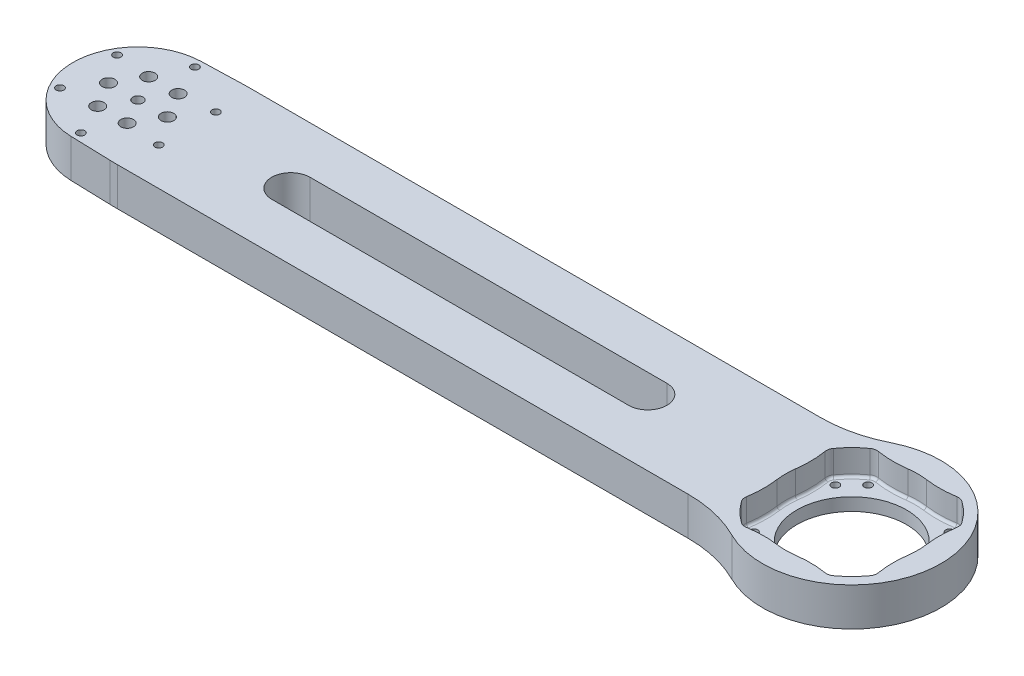
SolidWorks part; units mm, degrees
ref_plane "前视基准面" through (0, 0, 0) normal (0, 0, 1) x (1, 0, 0)
ref_plane "上视基准面" through (0, 0, 0) normal (0, 1, 0) x (1, 0, 0)
ref_plane "右视基准面" through (0, 0, 0) normal (1, 0, 0) x (0, 0, -1)
sketch "草图1" plane through (0, 0, 0) normal (0, 1, 0) x (1, 0, 0)
  line L0 (21.6852, 20) -> (239.1956, 20)
  line L1 (21.6852, -20) -> (239.1956, -20)
  line L2 (280, 35) -> (280, -35) construction
  line L3 (245, 0) -> (315, 0) construction
  line L4 (302.3882, -15.9693) -> (280, 0) construction
  line L5 (264.0307, 22.3882) -> (280, 0) construction
  line L8 (60, 0) -> (200, 0) construction
  line L9 (60, 7.5) -> (200, 7.5)
  line L10 (60, -7.5) -> (200, -7.5)
  line L11 (21.6852, 20) -> (21.6852, -20) construction
  circle A0 centre (0, 0) radius 25.5 construction
  circle A2 centre (280, 0) radius 35 construction
  circle A3 centre (280, 0) radius 27.5 construction
  circle A4 centre (302.3882, -15.9693) radius 1.5
  circle A5 centre (264.0307, 22.3882) radius 1.5
  circle A6 centre (302.3882, 15.9693) radius 1.5
  circle A7 centre (264.0307, -22.3882) radius 1.5
  circle A8 centre (280, 0) radius 35 construction
  circle A9 centre (295.9693, -22.3882) radius 1.5
  circle A10 centre (257.6118, 15.9693) radius 1.5
  circle A11 centre (280, 0) radius 35 construction
  circle A12 centre (257.6118, -15.9693) radius 1.5
  circle A13 centre (295.9693, 22.3882) radius 1.5
  circle A14 centre (280, 0) radius 35 construction
  circle A15 centre (280, 0) radius 21.5
  arc A18 (12.1533, 22.4176) -> (12.1533, -22.4176) centre (0, 0) ccw
  circle A19 centre (0, 0) radius 2
  arc A22 (60, 7.5) -> (60, -7.5) centre (60, 0) ccw
  arc A23 (200, -7.5) -> (200, 7.5) centre (200, 0) ccw
  arc A25 (257.3309, 26.6667) -> (257.3309, -26.6667) centre (280, 0) cw
  arc A26 (239.1956, -20) -> (257.3309, -26.6667) centre (239.1956, -48) cw
  arc A27 (239.1956, 20) -> (257.3309, 26.6667) centre (239.1956, 48) ccw
  arc A28 (21.6852, -20) -> (12.1533, -22.4176) centre (21.6852, -40) ccw
  arc A29 (21.6852, 20) -> (12.1533, 22.4176) centre (21.6852, 40) cw
  point P4 (21.6852, 0)
  point P36 (280, 0)
  point P39 (251.2772, -20)
  point P40 (294.1494, 32.0124)
  point P43 (130, 0)
  point P55 (251.2772, 20)
  point P66 (15.8193, -20)
  point P69 (15.8193, 20)
  dimension "D1" = 51
  dimension "D2" = 70
  dimension "D3" = 55
  dimension "D6" = 3
  dimension "D8" = 43
  dimension "D11" = 20
  dimension "D12" = 4
  dimension "D14" = 40
  dimension "D9" = 280
  dimension "D10" = 28
  dimension "D4" = 54.5
  dimension "D5" = 54.5
  dimension "D13" = 130
  dimension "D16" = 15
  dimension "D17" = 140
  dimension "D7" = 4
extrude "凸台-拉伸1" add sketch "草图1" along normal blind 15
sketch "草图2" plane through (0, 15, 0) normal (0, 1, 0) x (1, 0, 0)
  circle A0 centre (0, 0) radius 11.547 construction
  circle A1 centre (-11.547, 0) radius 1.7908
sketch "草图3" plane through (0, 15, 0) normal (0, 1, 0) x (1, 0, 0)
  circle A0 centre (-5.7735, -10) radius 2.5 construction
  circle A1 centre (-5.7735, -10) radius 2.5
  circle A2 centre (-11.547, 0) radius 2.5
  circle A3 centre (-5.7735, 10) radius 2.5
  circle A4 centre (5.7735, 10) radius 2.5
  circle A5 centre (11.547, 0) radius 2.5
  circle A6 centre (5.7735, -10) radius 2.5
  circle A7 centre (0, -22.375) radius 1.5
  circle A8 centre (-19.3773, -11.1875) radius 1.5
  circle A9 centre (-19.3773, 11.1875) radius 1.5
  circle A10 centre (0, 22.375) radius 1.5
  circle A11 centre (19.3773, 11.1875) radius 1.5
  circle A12 centre (19.3773, -11.1875) radius 1.5
  point P15 (0, 0)
  point P29 (0, 0)
  dimension "D1" = 6
  dimension "D2" = 6
extrude "切除-拉伸1" cut sketch "草图3" against normal through all
sketch "草图4" plane through (0, 15, 0) normal (0, 1, 0) x (1, 0, 0)
  arc A0 (283.6096, 25.6977) -> (295.3982, 25.8413) centre (289.0345, 64.3186) ccw
  arc A1 (295.9693, 25.8882) -> (295.3982, 25.8413) centre (295.9693, 22.3882) ccw
  arc A2 (298.0018, 25.2376) -> (295.9693, 25.8882) centre (295.9693, 22.3882) ccw
  arc A3 (305.2376, 18.0018) -> (298.0018, 25.2376) centre (280, 0) ccw
  arc A4 (305.8413, 15.3982) -> (305.2376, 18.0018) centre (302.3882, 15.9693) ccw
  arc A5 (305.8413, 15.3982) -> (305.6977, 3.6096) centre (344.3186, 9.0345) ccw
  arc A6 (305.6977, -3.6096) -> (305.6977, 3.6096) centre (280, 0) ccw
  arc A7 (305.6977, -3.6096) -> (305.8413, -15.3982) centre (344.3186, -9.0345) ccw
  arc A8 (305.2376, -18.0018) -> (305.8413, -15.3982) centre (302.3882, -15.9693) ccw
  arc A9 (298.0018, -25.2376) -> (305.2376, -18.0018) centre (280, 0) ccw
  arc A10 (295.3982, -25.8413) -> (298.0018, -25.2376) centre (295.9693, -22.3882) ccw
  arc A11 (295.3982, -25.8413) -> (289.0345, -25.3186) centre (289.0345, -64.3186) ccw
  arc A12 (289.0345, -25.3186) -> (283.6096, -25.6977) centre (289.0345, -64.3186) ccw
  arc A13 (276.3904, -25.6977) -> (283.6096, -25.6977) centre (280, 0) ccw
  arc A14 (276.3904, -25.6977) -> (270.9655, -25.3186) centre (270.9655, -64.3186) ccw
  arc A15 (270.9655, -25.3186) -> (264.6018, -25.8413) centre (270.9655, -64.3186) ccw
  arc A16 (261.9982, -25.2376) -> (264.6018, -25.8413) centre (264.0307, -22.3882) ccw
  arc A17 (254.7624, -18.0018) -> (261.9982, -25.2376) centre (280, 0) ccw
  arc A18 (254.1587, -15.3982) -> (254.7624, -18.0018) centre (257.6118, -15.9693) ccw
  arc A19 (254.1587, -15.3982) -> (254.3023, -3.6096) centre (215.6814, -9.0345) ccw
  arc A20 (254.3023, 3.6096) -> (254.3023, -3.6096) centre (280, 0) ccw
  arc A21 (254.3023, 3.6096) -> (254.1587, 15.3982) centre (215.6814, 9.0345) ccw
  arc A22 (254.7624, 18.0018) -> (254.1587, 15.3982) centre (257.6118, 15.9693) ccw
  arc A23 (261.9982, 25.2376) -> (254.7624, 18.0018) centre (280, 0) ccw
  arc A24 (264.0307, 25.8882) -> (261.9982, 25.2376) centre (264.0307, 22.3882) ccw
  arc A25 (264.6018, 25.8413) -> (264.0307, 25.8882) centre (264.0307, 22.3882) ccw
  arc A26 (264.6018, 25.8413) -> (276.3904, 25.6977) centre (270.9655, 64.3186) ccw
  arc A27 (280, 25.95) -> (276.3904, 25.6977) centre (280, 0) ccw
  arc A28 (283.6096, 25.6977) -> (280, 25.95) centre (280, 0) ccw
  arc A29 (283.4705, 24.7074) -> (295.5614, 24.8547) centre (289.0345, 64.3186) ccw
  arc A30 (295.9693, 24.8882) -> (295.5614, 24.8547) centre (295.9693, 22.3882) ccw
  arc A31 (297.4211, 24.4235) -> (295.9693, 24.8882) centre (295.9693, 22.3882) ccw
  arc A32 (304.4235, 17.4211) -> (297.4211, 24.4235) centre (280, 0) ccw
  arc A33 (304.8547, 15.5614) -> (304.4235, 17.4211) centre (302.3882, 15.9693) ccw
  arc A34 (304.8547, 15.5614) -> (304.7074, 3.4705) centre (344.3186, 9.0345) ccw
  arc A35 (304.7074, -3.4705) -> (304.7074, 3.4705) centre (280, 0) ccw
  arc A36 (304.7074, -3.4705) -> (304.8547, -15.5614) centre (344.3186, -9.0345) ccw
  arc A37 (304.4235, -17.4211) -> (304.8547, -15.5614) centre (302.3882, -15.9693) ccw
  arc A38 (297.4211, -24.4235) -> (304.4235, -17.4211) centre (280, 0) ccw
  arc A39 (295.5614, -24.8547) -> (297.4211, -24.4235) centre (295.9693, -22.3882) ccw
  arc A40 (295.5614, -24.8547) -> (289.0345, -24.3186) centre (289.0345, -64.3186) ccw
  arc A41 (289.0345, -24.3186) -> (283.4705, -24.7074) centre (289.0345, -64.3186) ccw
  arc A42 (276.5295, -24.7074) -> (283.4705, -24.7074) centre (280, 0) ccw
  arc A43 (276.5295, -24.7074) -> (270.9655, -24.3186) centre (270.9655, -64.3186) ccw
  arc A44 (270.9655, -24.3186) -> (264.4386, -24.8547) centre (270.9655, -64.3186) ccw
  arc A45 (262.5789, -24.4235) -> (264.4386, -24.8547) centre (264.0307, -22.3882) ccw
  arc A46 (255.5765, -17.4211) -> (262.5789, -24.4235) centre (280, 0) ccw
  arc A47 (255.1453, -15.5614) -> (255.5765, -17.4211) centre (257.6118, -15.9693) ccw
  arc A48 (255.1453, -15.5614) -> (255.2926, -3.4705) centre (215.6814, -9.0345) ccw
  arc A49 (255.2926, 3.4705) -> (255.2926, -3.4705) centre (280, 0) ccw
  arc A50 (255.2926, 3.4705) -> (255.1453, 15.5614) centre (215.6814, 9.0345) ccw
  arc A51 (255.5765, 17.4211) -> (255.1453, 15.5614) centre (257.6118, 15.9693) ccw
  arc A52 (262.5789, 24.4235) -> (255.5765, 17.4211) centre (280, 0) ccw
  arc A53 (264.0307, 24.8882) -> (262.5789, 24.4235) centre (264.0307, 22.3882) ccw
  arc A54 (264.4386, 24.8547) -> (264.0307, 24.8882) centre (264.0307, 22.3882) ccw
  arc A55 (264.4386, 24.8547) -> (276.5295, 24.7074) centre (270.9655, 64.3186) ccw
  arc A56 (280, 24.95) -> (276.5295, 24.7074) centre (280, 0) ccw
  arc A57 (283.4705, 24.7074) -> (280, 24.95) centre (280, 0) ccw
  arc A58 (283.4705, 24.7074) -> (295.5614, 24.8547) centre (289.0345, 64.3186) ccw construction
  arc A59 (295.9693, 24.8882) -> (295.5614, 24.8547) centre (295.9693, 22.3882) ccw construction
  arc A60 (297.4211, 24.4235) -> (295.9693, 24.8882) centre (295.9693, 22.3882) ccw construction
  arc A61 (304.4235, 17.4211) -> (297.4211, 24.4235) centre (280, 0) ccw construction
  arc A62 (304.8547, 15.5614) -> (304.4235, 17.4211) centre (302.3882, 15.9693) ccw construction
  arc A63 (304.8547, 15.5614) -> (304.7074, 3.4705) centre (344.3186, 9.0345) ccw construction
  arc A64 (304.7074, -3.4705) -> (304.7074, 3.4705) centre (280, 0) ccw construction
  arc A65 (304.7074, -3.4705) -> (304.8547, -15.5614) centre (344.3186, -9.0345) ccw construction
  arc A66 (304.4235, -17.4211) -> (304.8547, -15.5614) centre (302.3882, -15.9693) ccw construction
  arc A67 (297.4211, -24.4235) -> (304.4235, -17.4211) centre (280, 0) ccw construction
  arc A68 (295.5614, -24.8547) -> (297.4211, -24.4235) centre (295.9693, -22.3882) ccw construction
  arc A69 (295.5614, -24.8547) -> (289.0345, -24.3186) centre (289.0345, -64.3186) ccw construction
  arc A70 (289.0345, -24.3186) -> (283.4705, -24.7074) centre (289.0345, -64.3186) ccw construction
  arc A71 (276.5295, -24.7074) -> (283.4705, -24.7074) centre (280, 0) ccw construction
  arc A72 (276.5295, -24.7074) -> (270.9655, -24.3186) centre (270.9655, -64.3186) ccw construction
  arc A73 (270.9655, -24.3186) -> (264.4386, -24.8547) centre (270.9655, -64.3186) ccw construction
  arc A74 (262.5789, -24.4235) -> (264.4386, -24.8547) centre (264.0307, -22.3882) ccw construction
  arc A75 (255.5765, -17.4211) -> (262.5789, -24.4235) centre (280, 0) ccw construction
  arc A76 (255.1453, -15.5614) -> (255.5765, -17.4211) centre (257.6118, -15.9693) ccw construction
  arc A77 (255.1453, -15.5614) -> (255.2926, -3.4705) centre (215.6814, -9.0345) ccw construction
  arc A78 (255.2926, 3.4705) -> (255.2926, -3.4705) centre (280, 0) ccw construction
  arc A79 (255.2926, 3.4705) -> (255.1453, 15.5614) centre (215.6814, 9.0345) ccw construction
  arc A80 (255.5765, 17.4211) -> (255.1453, 15.5614) centre (257.6118, 15.9693) ccw construction
  arc A81 (262.5789, 24.4235) -> (255.5765, 17.4211) centre (280, 0) ccw construction
  arc A82 (264.0307, 24.8882) -> (262.5789, 24.4235) centre (264.0307, 22.3882) ccw construction
  arc A83 (264.4386, 24.8547) -> (264.0307, 24.8882) centre (264.0307, 22.3882) ccw construction
  arc A84 (264.4386, 24.8547) -> (276.5295, 24.7074) centre (270.9655, 64.3186) ccw construction
  arc A85 (280, 24.95) -> (276.5295, 24.7074) centre (280, 0) ccw construction
  arc A86 (283.4705, 24.7074) -> (280, 24.95) centre (280, 0) ccw construction
  dimension "D1" = 0
  dimension "D2" = 1
extrude "切除-拉伸2" cut sketch "草图4" against normal blind 10
fillet "圆角1" radius 1 24 edges at (263.2401, 5, -25.7977) (270.4906, 5, -25.3215) (280, 5, -25.95) (289.5094, 5, -25.3215) (296.7599, 5, -25.7977) (301.9203, 5, -21.9203) (305.7977, 5, -16.7599) (305.3215, 5, -9.5094) (305.95, 5, 0) (305.3215, 5, 9.5094) (305.7977, 5, 16.7599) (301.9203, 5, 21.9203) (296.7599, 5, 25.7977) (289.5094, 5, 25.3215) (280, 5, 25.95) (270.4906, 5, 25.3215) (263.2401, 5, 25.7977) (258.0797, 5, 21.9203) (254.2023, 5, 16.7599) (254.6785, 5, 9.5094) (254.05, 5, 0) (254.6785, 5, -9.5094) (254.2023, 5, -16.7599) (258.0797, 5, -21.9203)
sketch "草图5" plane through (0, 15, 0) normal (0, 1, 0) x (1, 0, 0)
  line L0 (-0.7551, -25.4888) -> (15.0197, -25.9561)
  line L1 (0, 0) -> (-40.6702, 0) construction
  line L2 (17.9809, -26) -> (241.8548, -26)
  line L3 (-0.7551, 25.4888) -> (15.0197, 25.9561)
  line L4 (17.9809, 26) -> (241.8548, 26)
  line L5 (60, -7.5) -> (200, -7.5) construction
  line L6 (200, 7.5) -> (60, 7.5) construction
  line L7 (60, -7.5) -> (200, -7.5)
  line L8 (200, 7.5) -> (60, 7.5)
  arc A0 (-0.7551, -25.4888) -> (-0.7551, 25.4888) centre (0, 0) cw
  arc A1 (12.1533, 22.4176) -> (12.1533, -22.4176) centre (0, 0) ccw construction
  arc A2 (15.0197, -25.9561) -> (17.9809, -26) centre (17.9809, 74) ccw
  arc A3 (257.3309, -26.6667) -> (239.1956, -20) centre (239.1956, -48) ccw construction
  arc A4 (264.2838, 31.3128) -> (264.2838, -31.3128) centre (280, 0) cw
  arc A5 (200, -7.5) -> (200, 7.5) centre (200, 0) ccw construction
  arc A6 (60, 7.5) -> (60, -7.5) centre (60, 0) ccw construction
  arc A7 (257.3309, -26.6667) -> (257.3309, 26.6667) centre (280, 0) ccw construction
  arc A8 (241.8548, -26) -> (264.2838, -31.3128) centre (241.8548, -76) cw
  arc A9 (241.8548, 26) -> (264.2838, 31.3128) centre (241.8548, 76) ccw
  arc A10 (200, -7.5) -> (200, 7.5) centre (200, 0) ccw
  arc A11 (60, 7.5) -> (60, -7.5) centre (60, 0) ccw
  circle A12 centre (0, -22.375) radius 1.5 construction
  circle A13 centre (-19.3773, -11.1875) radius 1.5 construction
  circle A14 centre (-5.7735, -10) radius 2.5 construction
  circle A15 centre (19.3773, -11.1875) radius 1.5 construction
  circle A16 centre (5.7735, -10) radius 2.5 construction
  circle A17 centre (11.547, 0) radius 2.5 construction
  circle A18 centre (0, 0) radius 2 construction
  circle A19 centre (-11.547, 0) radius 2.5 construction
  circle A20 centre (-19.3773, 11.1875) radius 1.5 construction
  circle A21 centre (-5.7735, 10) radius 2.5 construction
  circle A22 centre (5.7735, 10) radius 2.5 construction
  circle A23 centre (19.3773, 11.1875) radius 1.5 construction
  circle A24 centre (0, 22.375) radius 1.5 construction
  circle A25 centre (0, -22.375) radius 1.5
  circle A26 centre (-19.3773, -11.1875) radius 1.5
  circle A27 centre (-5.7735, -10) radius 2.5
  circle A28 centre (19.3773, -11.1875) radius 1.5
  circle A29 centre (5.7735, -10) radius 2.5
  circle A30 centre (11.547, 0) radius 2.5
  circle A31 centre (0, 0) radius 2
  circle A32 centre (-11.547, 0) radius 2.5
  circle A33 centre (-19.3773, 11.1875) radius 1.5
  circle A34 centre (-5.7735, 10) radius 2.5
  circle A35 centre (5.7735, 10) radius 2.5
  circle A36 centre (19.3773, 11.1875) radius 1.5
  circle A37 centre (0, 22.375) radius 1.5
  circle A38 centre (280, 0) radius 32.0356
  arc A39 (15.0197, 25.9561) -> (17.9809, 26) centre (17.9809, -74) cw
  point P14 (16.5, -26)
  point P20 (16.5, 26)
  point P28 (256.5161, -26)
  point P31 (256.5161, 26)
  point P78 (0, 0)
  dimension "D1" = 100
  dimension "D2" = 50
  dimension "D3" = 3
extrude "凸台-拉伸2" add sketch "草图5" against normal up to surface (15 mm away) up to face at (-19.3773, 0, -9.6875)
